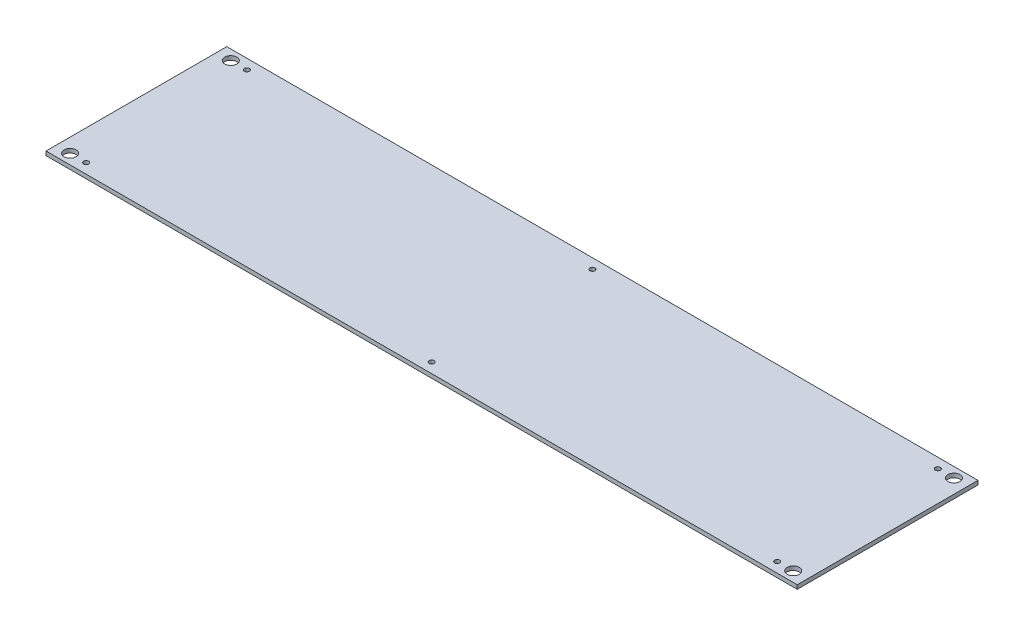
SolidWorks part; units mm, degrees
ref_plane "Front Plane" through (0, 0, 0) normal (0, 0, 1) x (1, 0, 0)
ref_plane "Top Plane" through (0, 0, 0) normal (0, 1, 0) x (1, 0, 0)
ref_plane "Right Plane" through (0, 0, 0) normal (1, 0, 0) x (0, 0, -1)
sketch "Sketch1" plane through (0, 0, 0) normal (0, 1, 0) x (1, 0, 0)
  line L0 (0, 90) -> (0, -90) construction
  line L1 (-374, -90) -> (374, -90)
  line L2 (-374, -90) -> (-374, 90)
  line L3 (-374, 90) -> (374, 90)
  line L4 (374, -90) -> (374, 90)
  line L5 (-374, -90) -> (374, 90) construction
  line L6 (-374, 90) -> (374, -90) construction
  line L7 (-374, 0) -> (374, 0) construction
  circle A0 centre (-344, 80) radius 2.5
  circle A1 centre (0, 80) radius 2.5
  circle A2 centre (344, 80) radius 2.5
  circle A3 centre (-344, -80) radius 2.5
  circle A4 centre (0, -80) radius 2.5
  circle A5 centre (344, -80) radius 2.5
  circle A6 centre (-360, 80) radius 6
  circle A7 centre (-360, -80) radius 6
  circle A8 centre (360, -80) radius 6
  circle A9 centre (360, 80) radius 6
  point P0 (0, 0)
  dimension "D3" = 5
  dimension "D4" = 5
  dimension "D7" = 30
  dimension "D8" = 12
  dimension "D1" = 180
  dimension "D2" = 748
  dimension "D5" = 10
  dimension "D6" = 10
  dimension "D9" = 10
  dimension "D10" = 14
extrude "Boss-Extrude1" add sketch "Sketch1" along normal blind 4
